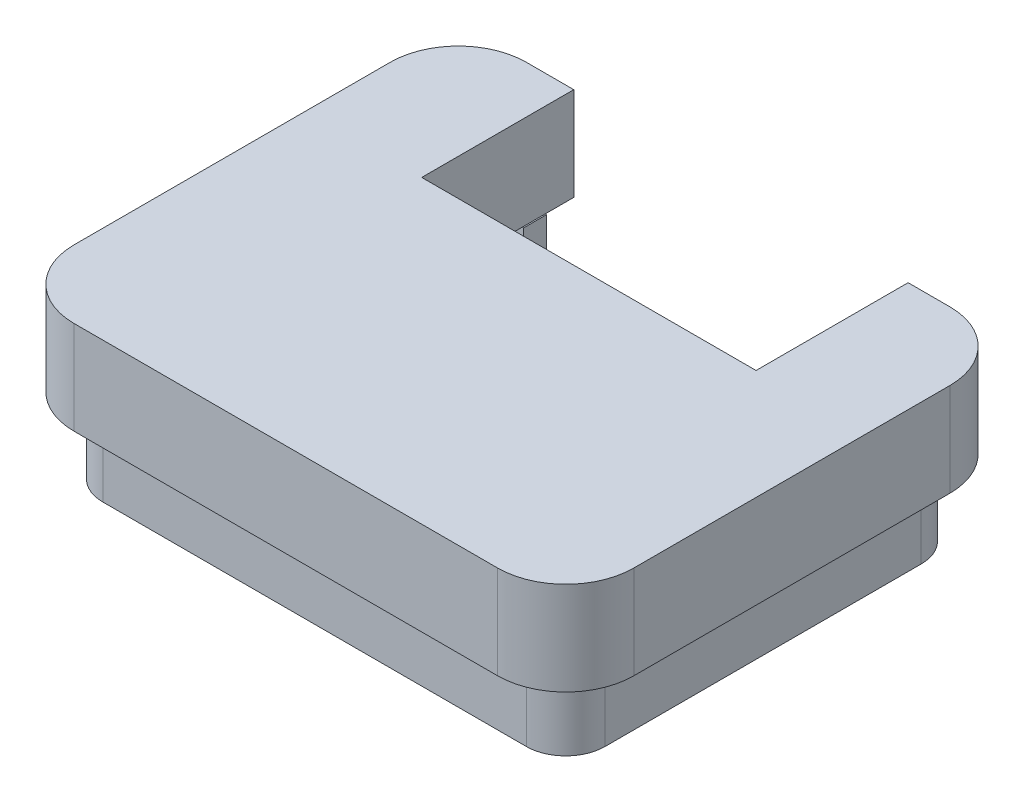
SolidWorks part; units mm, degrees
ref_plane "前视基准面" through (0, 0, 0) normal (0, 0, 1) x (1, 0, 0)
ref_plane "上视基准面" through (0, 0, 0) normal (0, 1, 0) x (1, 0, 0)
ref_plane "右视基准面" through (0, 0, 0) normal (1, 0, 0) x (0, 0, -1)
sketch "草图2" plane through (0, 15, 0) normal (0, 1, 0) x (1, 0, 0)
  line L24 (0, 0.4115) -> (-27.986, 0.4115) construction
  line L26 (-24.8533, 10.4615) -> (-24.8533, 0.4115)
  line L27 (-24.8533, 0.4115) -> (-2.7533, 0.4115)
  line L36 (-2.7533, 10.4615) -> (-2.7533, 0.4115)
  line L45 (-27.986, 8.9615) -> (-24.8533, 8.9615)
  line L62 (-24.8533, 8.9615) -> (-24.8533, 10.4615)
  line L63 (-24.8533, 10.4615) -> (-27.986, 10.4615)
  line L64 (-32.486, 5.9615) -> (-32.486, -14.9385)
  line L65 (-27.986, -19.4385) -> (0.014, -19.4385)
  line L66 (4.514, -14.9385) -> (4.514, 5.9615)
  line L67 (0.014, 10.4615) -> (-2.7533, 10.4615)
  line L68 (-2.7533, 10.4615) -> (-2.7533, 8.9615)
  line L69 (-2.7533, 8.9615) -> (0.014, 8.9615)
  line L70 (3.014, 5.9615) -> (3.014, -14.9385)
  line L71 (0.014, -17.9385) -> (-27.986, -17.9385)
  line L72 (-30.986, -14.9385) -> (-30.986, 5.9615)
  line L75 (-24.8533, 10.4615) -> (-27.986, 10.4615)
  line L76 (-32.486, 5.9615) -> (-32.486, -14.9385)
  line L77 (-27.986, -19.4385) -> (0.014, -19.4385)
  line L78 (4.514, -14.9385) -> (4.514, 5.9615)
  line L79 (0.014, 10.4615) -> (-2.7533, 10.4615)
  arc A28 (-27.986, 10.4615) -> (-32.486, 5.9615) centre (-27.986, 5.9615) ccw
  arc A29 (-32.486, -14.9385) -> (-27.986, -19.4385) centre (-27.986, -14.9385) ccw
  arc A30 (0.014, -19.4385) -> (4.514, -14.9385) centre (0.014, -14.9385) ccw
  arc A31 (4.514, 5.9615) -> (0.014, 10.4615) centre (0.014, 5.9615) ccw
  arc A32 (3.014, 5.9615) -> (0.014, 8.9615) centre (0.014, 5.9615) ccw
  arc A33 (0.014, -17.9385) -> (3.014, -14.9385) centre (0.014, -14.9385) ccw
  arc A34 (-30.986, -14.9385) -> (-27.986, -17.9385) centre (-27.986, -14.9385) ccw
  arc A35 (-27.986, 8.9615) -> (-30.986, 5.9615) centre (-27.986, 5.9615) ccw
  arc A36 (-27.986, 10.4615) -> (-32.486, 5.9615) centre (-27.986, 5.9615) ccw
  arc A38 (-32.486, -14.9385) -> (-27.986, -19.4385) centre (-27.986, -14.9385) ccw
  arc A40 (0.014, -19.4385) -> (4.514, -14.9385) centre (0.014, -14.9385) ccw
  arc A42 (4.514, 5.9615) -> (0.014, 10.4615) centre (0.014, 5.9615) ccw
  dimension "D1" = 0
extrude "凸台-拉伸3" add sketch "草图2" along normal up to surface (1.1699 mm away)
sketch "草图4" plane through (0, 15, 0) normal (0, -1, 0) x (1, 0, 0)
  line L4 (-14.193, 0.2) -> (-14.193, -49999.8) construction
  line L5 (-23.193, 0.4) -> (-28.386, 0.4)
  line L7 (-23.193, 0.4) -> (-23.193, 3.4)
  line L8 (-27.986, -10.4615) -> (-24.8533, -10.4615)
  line L9 (-24.8533, -10.4615) -> (-24.8533, -0.4115)
  line L10 (-24.8533, -0.4115) -> (-2.7533, -0.4115)
  line L11 (-2.7533, -0.4115) -> (-2.7533, -10.4615)
  line L12 (-2.7533, -10.4615) -> (0.014, -10.4615)
  line L13 (4.514, -5.9615) -> (4.514, 14.9385)
  line L14 (0.014, 19.4385) -> (-27.986, 19.4385)
  line L15 (-32.486, 14.9385) -> (-32.486, -5.9615)
  line L16 (-27.986, -10.4615) -> (-24.8533, -10.4615)
  line L17 (-24.8533, -10.4615) -> (-24.8533, -0.8115)
  line L19 (-2.7533, -0.8115) -> (-2.7533, -10.4615)
  line L20 (-2.7533, -10.4615) -> (0.014, -10.4615)
  line L21 (4.514, -5.9615) -> (4.514, 14.9385)
  line L22 (0.014, 19.4385) -> (-27.986, 19.4385)
  line L23 (-32.486, 14.9385) -> (-32.486, -5.9615)
  line L24 (-28.386, 0.4) -> (-28.386, -0.8115)
  line L25 (-28.386, -0.8115) -> (0.4, -0.8115)
  line L26 (0.4, -0.8115) -> (0.4, 0.4)
  line L27 (0.4, 0.4) -> (-28.386, 0.4)
  line L28 (-28.386, 0.4) -> (-28.386, -0.8115)
  line L29 (-28.386, -0.8115) -> (-24.8533, -0.8115)
  line L30 (0.4, -0.8115) -> (0.4, 0.4)
  line L31 (0.4, 0.4) -> (-5.193, 0.4)
  line L32 (-23.193, 3.4) -> (-5.193, 3.4)
  line L33 (-5.193, 0.4) -> (-5.193, 3.4)
  line L34 (-2.7533, -0.8115) -> (0.4, -0.8115)
  arc A4 (0.014, -10.4615) -> (4.514, -5.9615) centre (0.014, -5.9615) ccw
  arc A5 (4.514, 14.9385) -> (0.014, 19.4385) centre (0.014, 14.9385) ccw
  arc A6 (-27.986, 19.4385) -> (-32.486, 14.9385) centre (-27.986, 14.9385) ccw
  arc A7 (-32.486, -5.9615) -> (-27.986, -10.4615) centre (-27.986, -5.9615) ccw
  arc A8 (0.014, -10.4615) -> (4.514, -5.9615) centre (0.014, -5.9615) ccw
  arc A9 (4.514, 14.9385) -> (0.014, 19.4385) centre (0.014, 14.9385) ccw
  arc A10 (-27.986, 19.4385) -> (-32.486, 14.9385) centre (-27.986, 14.9385) ccw
  arc A11 (-32.486, -5.9615) -> (-27.986, -10.4615) centre (-27.986, -5.9615) ccw
  dimension "D3" = 3
  dimension "D4" = 9
  dimension "D5" = 9
  dimension "D6" = 5.193
  dimension "D1" = 0
  dimension "D2" = 0.4
extrude "凸台-拉伸4" add sketch "草图4" along normal blind 5
sketch "草图5" plane through (0, 10, 0) normal (0, -1, 0) x (1, 0, 0)
  line L0 (-2.7533, -8.5615) -> (0.014, -8.5615)
  line L1 (-27.986, -8.5615) -> (0.014, -8.5615) construction
  line L2 (-2.7533, -7.0615) -> (0.014, -7.0615)
  line L3 (-27.986, -7.0615) -> (0.014, -7.0615) construction
  line L4 (1.114, -5.9615) -> (1.114, 14.9385)
  line L5 (0.014, 16.0385) -> (-27.986, 16.0385)
  line L6 (-29.086, 14.9385) -> (-29.086, -5.9615)
  line L7 (-27.986, -7.0615) -> (-24.7682, -7.0615)
  line L8 (2.614, -5.9615) -> (2.614, 14.9385)
  line L9 (0.014, 17.5385) -> (-27.986, 17.5385)
  line L10 (-30.586, 14.9385) -> (-30.586, -5.9615)
  line L11 (-27.986, -8.5615) -> (0.014, -8.5615)
  line L12 (2.614, -5.9615) -> (2.614, 14.9385)
  line L13 (0.014, 17.5385) -> (-27.986, 17.5385)
  line L14 (-30.586, 14.9385) -> (-30.586, -5.9615)
  line L15 (-27.986, -8.5615) -> (-24.7682, -8.5615)
  line L16 (-2.7533, -8.5615) -> (-2.7533, -7.0615)
  line L17 (-2.7533, -0.8115) -> (-2.7533, -10.4615) construction
  line L18 (-24.7682, -8.5615) -> (-24.7682, -7.0615)
  arc A4 (1.114, 14.9385) -> (0.014, 16.0385) centre (0.014, 14.9385) ccw
  arc A5 (-27.986, 16.0385) -> (-29.086, 14.9385) centre (-27.986, 14.9385) ccw
  arc A6 (-29.086, -5.9615) -> (-27.986, -7.0615) centre (-27.986, -5.9615) ccw
  arc A7 (0.014, -7.0615) -> (1.114, -5.9615) centre (0.014, -5.9615) ccw
  arc A8 (2.614, 14.9385) -> (0.014, 17.5385) centre (0.014, 14.9385) ccw
  arc A9 (-27.986, 17.5385) -> (-30.586, 14.9385) centre (-27.986, 14.9385) ccw
  arc A10 (-30.586, -5.9615) -> (-27.986, -8.5615) centre (-27.986, -5.9615) ccw
  arc A11 (0.014, -8.5615) -> (2.614, -5.9615) centre (0.014, -5.9615) ccw
  arc A12 (2.614, 14.9385) -> (0.014, 17.5385) centre (0.014, 14.9385) ccw
  arc A13 (-27.986, 17.5385) -> (-30.586, 14.9385) centre (-27.986, 14.9385) ccw
  arc A14 (-30.586, -5.9615) -> (-27.986, -8.5615) centre (-27.986, -5.9615) ccw
  arc A15 (0.014, -8.5615) -> (2.614, -5.9615) centre (0.014, -5.9615) ccw
  dimension "D1" = 0.4
  dimension "D2" = 1.5
extrude "凸台-拉伸5" add sketch "草图5" along normal blind 5
